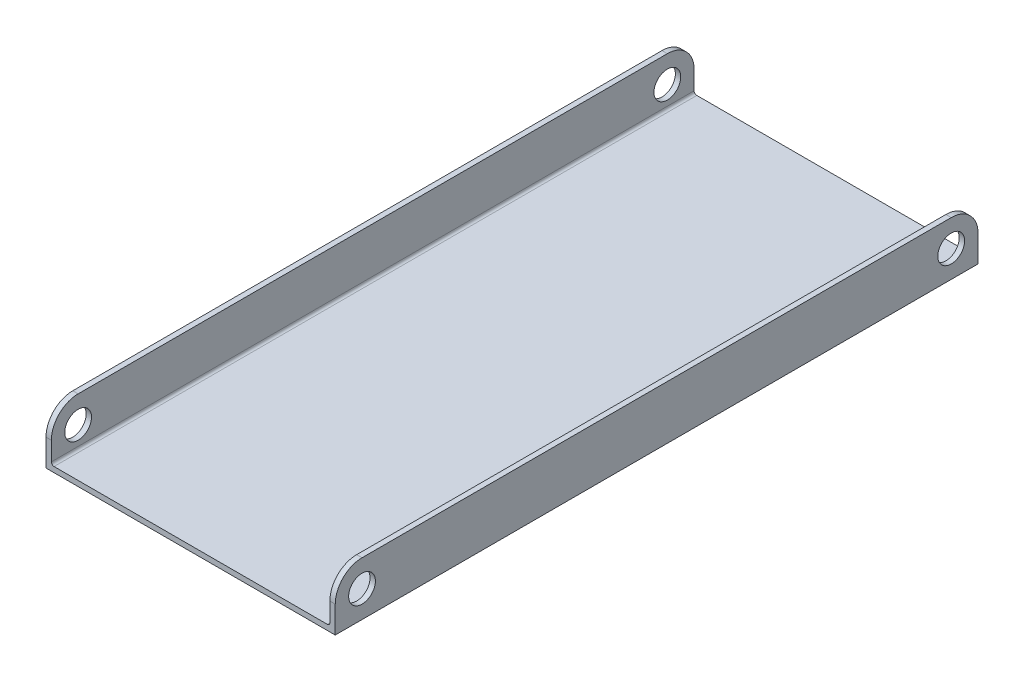
SolidWorks part; units mm, degrees
material "AISI 1020"
ref_plane "Front Plane" through (0, 0, 0) normal (0, 0, 1) x (1, 0, 0)
ref_plane "Top Plane" through (0, 0, 0) normal (0, 1, 0) x (1, 0, 0)
ref_plane "Right Plane" through (0, 0, 0) normal (1, 0, 0) x (0, 0, -1)
sketch "Sketch1" plane through (0, 0, 0) normal (0, 0, 1) x (1, 0, 0)
  line L0 (0, 0) -> (0, 9.8624) construction
  line L1 (-34.29, -6.35) -> (34.29, -6.35)
  line L2 (-34.29, -6.35) -> (-34.29, 6.35)
  line L3 (-34.29, 6.35) -> (34.29, 6.35)
  line L4 (34.29, -6.35) -> (34.29, 6.35)
  line L5 (-34.29, -6.35) -> (34.29, 6.35) construction
  line L6 (-34.29, 6.35) -> (34.29, -6.35) construction
  line L7 (-33.02, 6.35) -> (33.02, 6.35)
  line L8 (-33.02, 6.35) -> (-33.02, -5.08)
  line L9 (-33.02, -5.08) -> (33.02, -5.08)
  line L10 (33.02, 6.35) -> (33.02, -5.08)
  point P0 (0, 0)
  dimension "D1" = 12.7
  dimension "D2" = 68.58
  dimension "D3" = 66.04
  dimension "D4" = 1.27
extrude "Boss-Extrude1" add sketch "Sketch1" along normal blind 152.4 contours L3 L10 L9 L8 L2 L1 L4
sketch "Sketch2" plane through (34.29, 0, 0) normal (1, 0, 0) x (0, 0, -1)
  line L0 (-76.2, 6.35) -> (-76.2, -6.35) construction
  line L1 (-152.4, 6.35) -> (0, 6.35) construction
  line L2 (-152.4, -6.35) -> (-152.4, 6.35) construction
  line L3 (-152.4, -6.35) -> (0, -6.35) construction
  line L4 (-76.2, 0) -> (-91.7595, 0) construction
  line L5 (-152.4, 0) -> (-152.4, 6.35)
  line L6 (-152.4, 6.35) -> (-146.05, 6.35)
  line L7 (0, 0) -> (0, 6.35)
  line L8 (0, 6.35) -> (-6.35, 6.35)
  circle A0 centre (-146.05, 0) radius 3.175
  arc A1 (-146.05, 6.35) -> (-152.4, 0) centre (-146.05, 0) ccw
  circle A2 centre (-6.35, 0) radius 3.175
  arc A3 (0, 0) -> (-6.35, 6.35) centre (-6.35, 0) ccw
  dimension "D2" = 6.35
  dimension "D3" = 6.35
  dimension "D5" = 6.35
  dimension "D1" = 6.35
extrude "Cut-Extrude1" cut sketch "Sketch2" against normal through all
fillet "Fillet1" radius 0.635 2 edges at (33.02, -5.08, 76.2) (-33.02, -5.08, 76.2)
